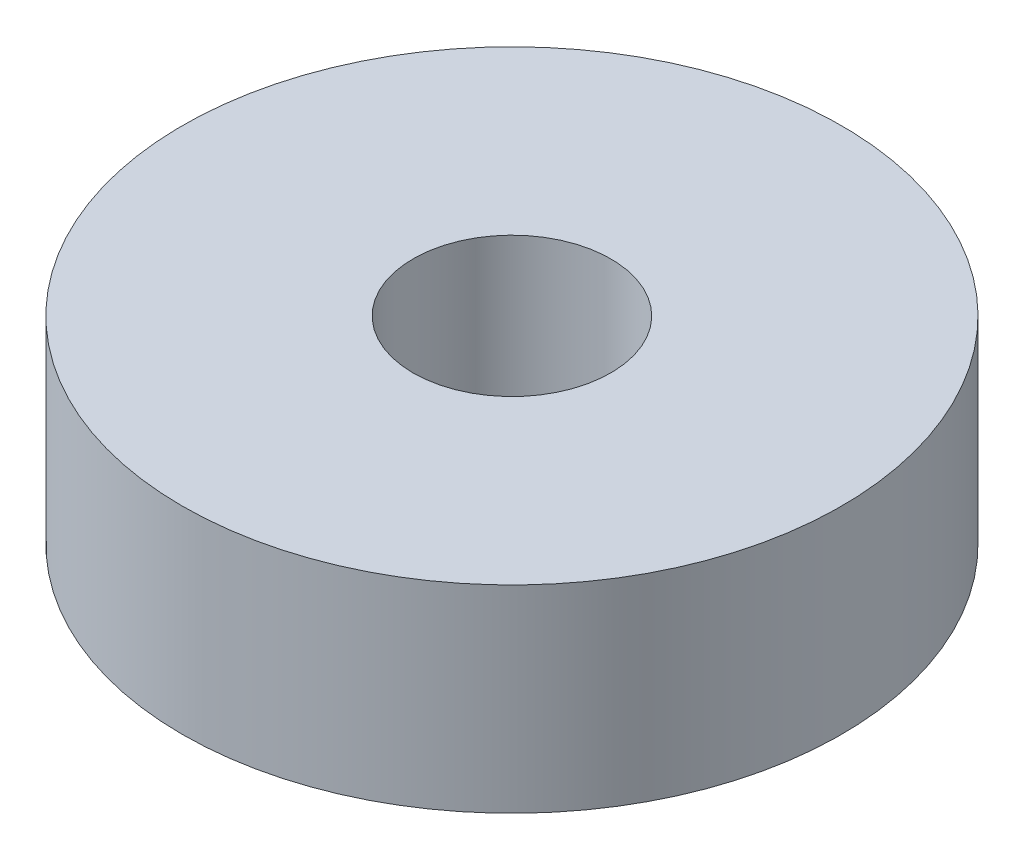
SolidWorks part; units mm, degrees
ref_plane "Front Plane" through (0, 0, 0) normal (0, 0, 1) x (1, 0, 0)
ref_plane "Top Plane" through (0, 0, 0) normal (0, 1, 0) x (1, 0, 0)
ref_plane "Right Plane" through (0, 0, 0) normal (1, 0, 0) x (0, 0, -1)
sketch "Sketch1" plane through (0, 0, 0) normal (0, 1, 0) x (1, 0, 0)
  circle A0 centre (0, 0) radius 5
  circle A1 centre (0, 0) radius 1.5
extrude "Boss-Extrude1" add sketch "Sketch1" along normal blind 3
